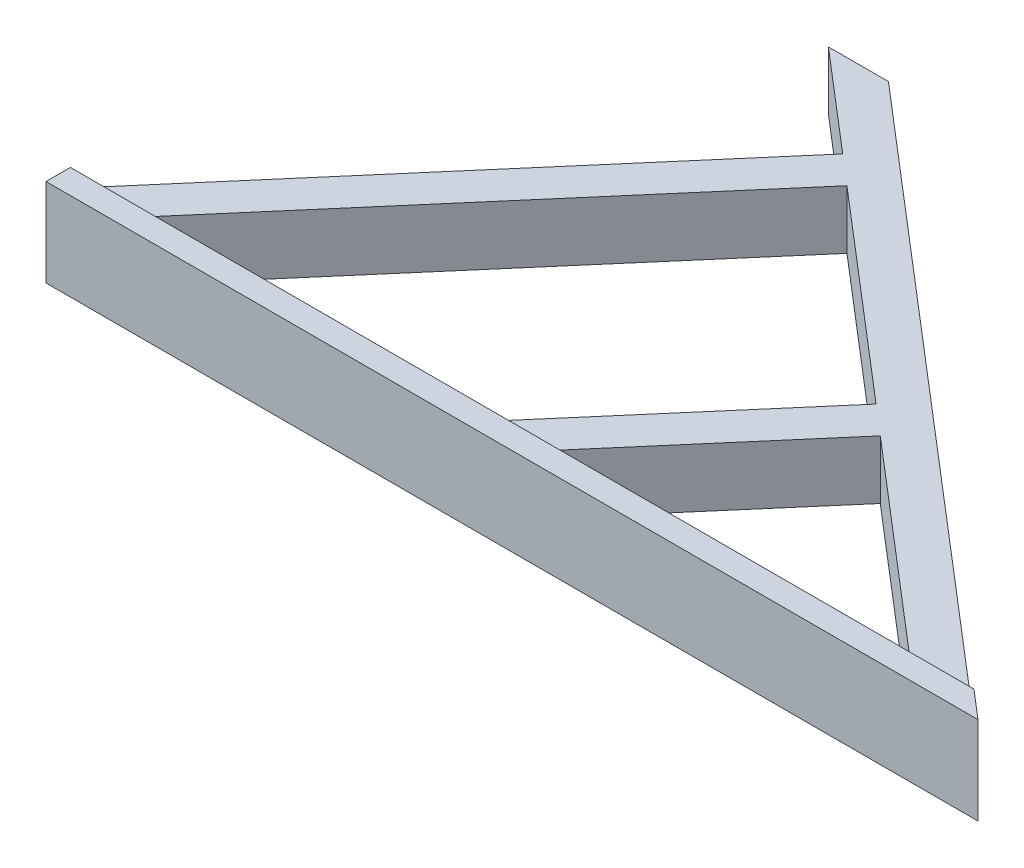
SolidWorks part; units mm, degrees
ref_plane "Alzado" through (0, 0, 0) normal (0, 0, 1) x (1, 0, 0)
ref_plane "Planta" through (0, 0, 0) normal (0, 1, 0) x (1, 0, 0)
ref_plane "Vista lateral" through (0, 0, 0) normal (1, 0, 0) x (0, 0, -1)
sketch "Croquis1" plane through (0, 0, 0) normal (0, 1, 0) x (1, 0, 0)
  line L0 (-23.461, 0) -> (12.7116, 0)
  line L1 (54.7338, 0) -> (33.5454, 18.1607)
  line L2 (-3.6022, 50) -> (2.5443, 50)
  line L3 (2.5443, 50) -> (66.7139, -5)
  line L4 (66.7139, -5) -> (-28.7292, -5)
  line L5 (-28.7292, -5) -> (-28.7292, 0)
  line L7 (30.5083, 20.7638) -> (12.7116, 0)
  line L8 (33.5454, 18.1607) -> (17.9798, 0)
  line L11 (6.618, 41.2402) -> (-28.7292, 0)
  line L12 (9.6551, 38.6371) -> (-23.461, 0)
  line L14 (30.5083, 20.7638) -> (9.6551, 38.6371)
  line L15 (17.9798, 0) -> (54.7338, 0)
  line L16 (6.618, 41.2402) -> (-3.6022, 50)
  point P3 (0, 0)
  dimension "D1" = 40.6
  dimension "D2" = 5
  dimension "D3" = 4
  dimension "D4" = 50
  dimension "D5" = 4
  dimension "D6" = 4
extrude "Saliente-Extruir1" add sketch "Croquis1" along normal blind 6
sketch "Croquis2" plane through (0, 6, 0) normal (0, 1, 0) x (1, 0, 0)
  line L0 (-28.7292, -5) -> (66.7139, -5)
  line L1 (66.7139, -5) -> (63.7971, -2.5)
  line L2 (66.7139, -5) -> (2.5443, 50) construction
  line L6 (-28.7292, -5) -> (-28.7292, -2.5)
  line L7 (-28.7292, 0) -> (-28.7292, -5) construction
  line L8 (-28.7292, -2.5) -> (63.7971, -2.5)
  dimension "D1" = 2.5
extrude "Saliente-Extruir2" add sketch "Croquis2" along normal blind 3
